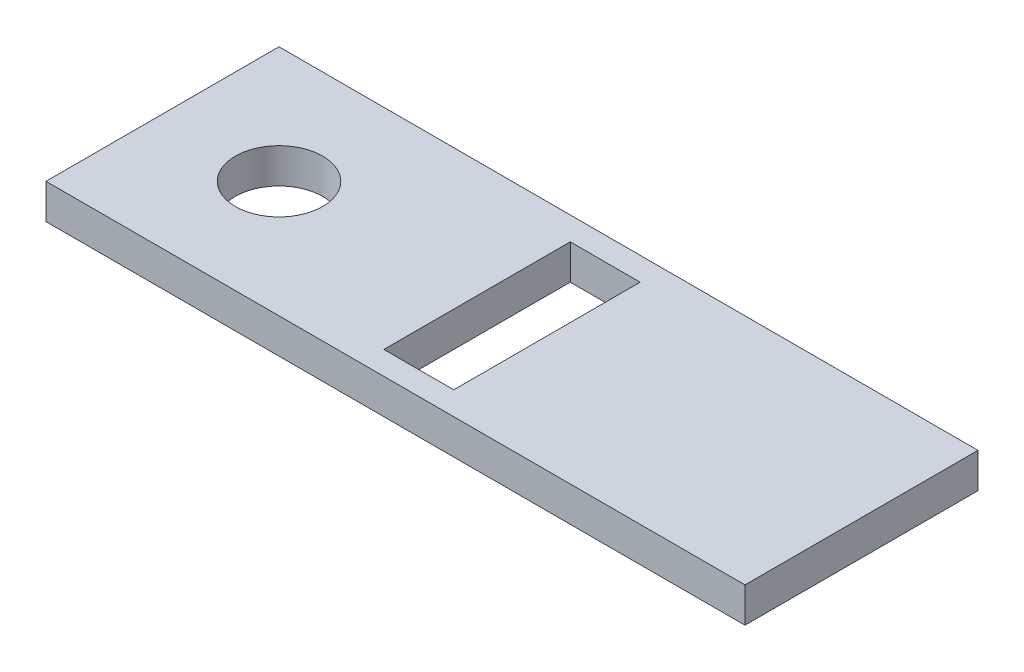
SolidWorks part; units mm, degrees
ref_plane "Front Plane" through (0, 0, 0) normal (0, 0, 1) x (1, 0, 0)
ref_plane "Top Plane" through (0, 0, 0) normal (0, 1, 0) x (1, 0, 0)
ref_plane "Right Plane" through (0, 0, 0) normal (1, 0, 0) x (0, 0, -1)
sketch "Sketch1" plane through (0, 0, 0) normal (0, 1, 0) x (1, 0, 0)
  line L1 (-76.2, -25.4) -> (76.2, -25.4)
  line L2 (-76.2, -25.4) -> (-76.2, 25.4)
  line L3 (-76.2, 25.4) -> (76.2, 25.4)
  line L4 (76.2, -25.4) -> (76.2, 25.4)
  line L5 (-76.2, -25.4) -> (76.2, 25.4) construction
  line L6 (-76.2, 25.4) -> (76.2, -25.4) construction
  point P0 (0, 0)
  dimension "D1" = 152.4
  dimension "D2" = 50.8
extrude "Boss-Extrude1" add sketch "Sketch1" along normal blind 7.62 contours L3 L4 L1 L2
sketch "Sketch2" plane through (0, 7.62, 0) normal (0, 1, 0) x (1, 0, 0)
  circle A0 centre (0, 0) radius 12.7
  dimension "D1" = 25.4
extrude "Cut-Extrude1" [suppressed] cut sketch "Sketch2" against normal through all
sketch "Sketch3" plane through (0, 7.62, 0) normal (0, 1, 0) x (1, 0, 0)
  line L0 (-76.2, -25.4) -> (-76.2, 25.4) construction
  circle A0 centre (-50.8, 0) radius 9.525
  dimension "D2" = 19.05
  dimension "D1" = 25.4
extrude "Cut-Extrude2" cut sketch "Sketch3" against normal through all
sketch "Sketch4" [suppressed] plane through (0, 7.62, 0) normal (0, 1, 0) x (1, 0, 0)
  line L0 (0, 25.4) -> (0, -25.4) construction
  line L1 (-76.2, 25.4) -> (76.2, 25.4) construction
  line L2 (-76.2, -25.4) -> (76.2, -25.4) construction
  circle A0 centre (-50.8, 0) radius 9.525 construction
  circle A1 centre (-50.8, 0) radius 9.525
  circle A2 centre (50.8, 0) radius 9.525
extrude "Cut-Extrude3" [suppressed] cut sketch "Sketch4" against normal through all contours A2
sketch "Sketch5" plane through (0, 7.62, 0) normal (0, 1, 0) x (1, 0, 0)
  line L1 (-7.62, -20.32) -> (7.62, -20.32)
  line L2 (-7.62, -20.32) -> (-7.62, 20.32)
  line L3 (-7.62, 20.32) -> (7.62, 20.32)
  line L4 (7.62, -20.32) -> (7.62, 20.32)
  line L5 (-7.62, -20.32) -> (7.62, 20.32) construction
  line L6 (-7.62, 20.32) -> (7.62, -20.32) construction
  point P0 (0, 0)
  dimension "D1" = 40.64
  dimension "D2" = 15.24
extrude "Cut-Extrude4" cut sketch "Sketch5" against normal through all
